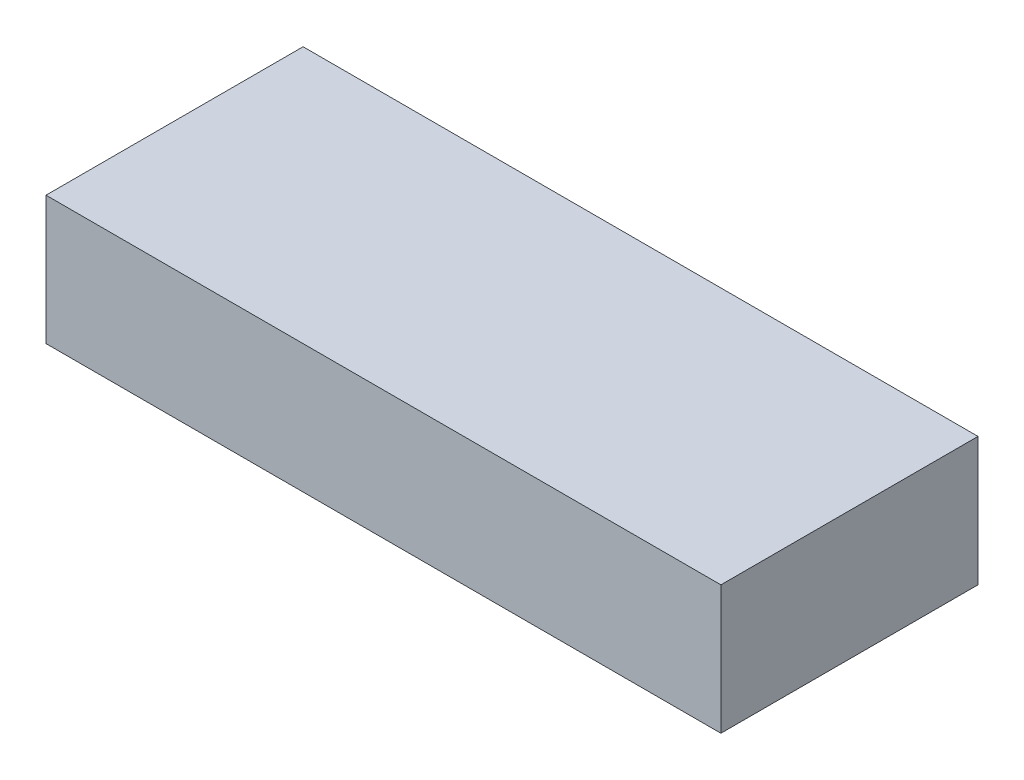
SolidWorks part; units mm, degrees
ref_plane "Front Plane" through (0, 0, 0) normal (0, 0, 1) x (1, 0, 0)
ref_plane "Top Plane" through (0, 0, 0) normal (0, 1, 0) x (1, 0, 0)
ref_plane "Right Plane" through (0, 0, 0) normal (1, 0, 0) x (0, 0, -1)
sketch "Sketch2" plane through (0, 0, 0) normal (0, 1, 0) x (1, 0, 0)
  line L1 (-66.675, -25.4) -> (66.675, -25.4)
  line L2 (-66.675, -25.4) -> (-66.675, 25.4)
  line L3 (-66.675, 25.4) -> (66.675, 25.4)
  line L4 (66.675, -25.4) -> (66.675, 25.4)
  line L5 (-66.675, -25.4) -> (66.675, 25.4) construction
  line L6 (-66.675, 25.4) -> (66.675, -25.4) construction
  point P0 (0, 0)
  dimension "D1" = 50.8
  dimension "D2" = 133.35
extrude "Boss-Extrude1" add sketch "Sketch2" along normal blind 25.4
